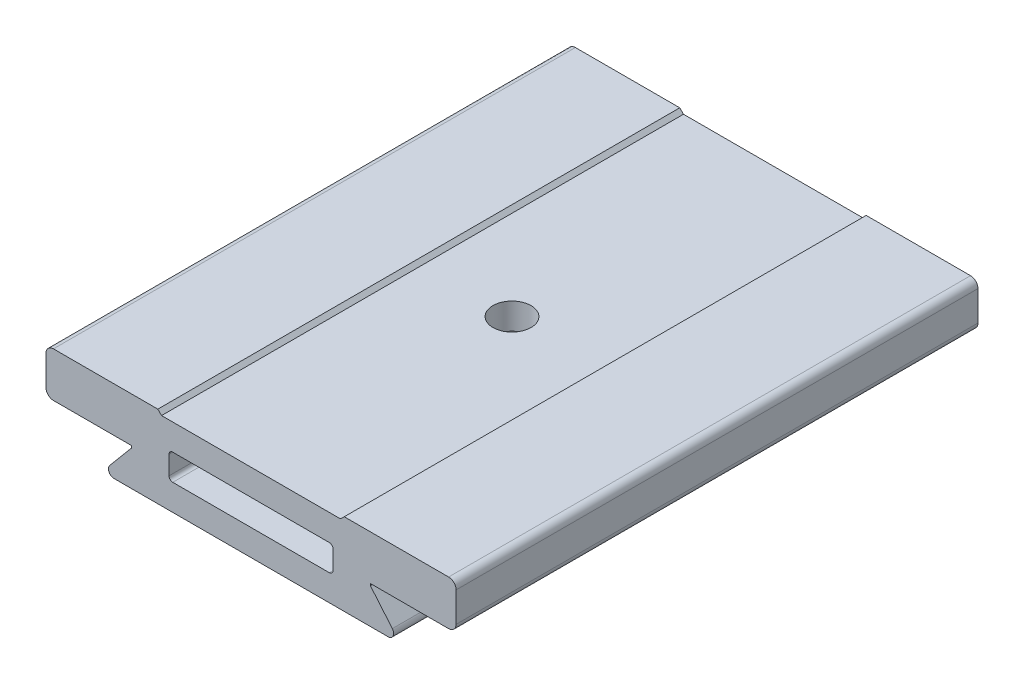
SolidWorks part; units mm, degrees
ref_plane "Front Plane" through (0, 0, 0) normal (0, 0, 1) x (1, 0, 0)
ref_plane "Top Plane" through (0, 0, 0) normal (0, 1, 0) x (1, 0, 0)
ref_plane "Right Plane" through (0, 0, 0) normal (1, 0, 0) x (0, 0, -1)
sketch "Sketch1" plane through (0, 0, 0) normal (0, 0, 1) x (1, 0, 0)
  line L1 (-27.5, 5.5) -> (27.5, 5.5)
  line L2 (-27.5, 5.5) -> (-27.5, -5.5)
  line L3 (-27.5, -5.5) -> (27.5, -5.5)
  line L4 (27.5, 5.5) -> (27.5, -5.5)
  line L5 (-27.5, 5.5) -> (27.5, -5.5) construction
  line L6 (-27.5, -5.5) -> (27.5, 5.5) construction
  point P0 (0, 0)
  dimension "D1" = 55
  dimension "D2" = 11
extrude "Boss-Extrude1" add sketch "Sketch1" along normal mid plane 70
sketch "Sketch2" plane through (0, 0, 35) normal (0, 0, 1) x (1, 0, 0)
  line L0 (-27.5, -0.5) -> (-16, -0.5)
  line L1 (-27.5, 5.5) -> (-27.5, -5.5) construction
  line L2 (-16, -0.5) -> (-16, -0.75)
  line L3 (-16, -0.75) -> (-18.9519, -4.2679)
  line L5 (-27.5, -5.5) -> (-18.3773, -5.5)
  line L6 (-27.5, -5.5) -> (-27.5, -0.5)
  line L7 (27.5, 5.5) -> (-27.5, 5.5) construction
  line L8 (-27.5, -5.5) -> (27.5, -5.5) construction
  arc A0 (-18.3773, -5.5) -> (-18.9519, -4.2679) centre (-18.3773, -4.75) cw
  dimension "D5" = 0.75
  dimension "D1" = 6
  dimension "D2" = 0.25
  dimension "D3" = 50
  dimension "D4" = 11.5
  dimension "D6" = 8.3727
extrude "Cut-Extrude1" cut sketch "Sketch2" against normal through all
mirror "Mirror1" about plane through (0, 0, 0) normal (1, 0, 0) of "Cut-Extrude1"
fillet "Fillet1" radius 1 4 edges at (27.5, 5.5, 0) (27.5, -0.5, 0) (-27.5, 5.5, 0) (-27.5, -0.5, 0)
sketch "Sketch3" plane through (0, 0, 35) normal (0, 0, 1) x (1, 0, 0)
  line L0 (0, 5.5) -> (0, -5.5) construction
  line L1 (26.5, 5.5) -> (-26.5, 5.5) construction
  line L2 (-18.3773, -5.5) -> (18.3773, -5.5) construction
  line L3 (-12.5, 5.5) -> (0, 5.5)
  line L4 (0, 5.5) -> (0, 5)
  line L5 (0, 5) -> (-12, 5)
  line L6 (-12, 5) -> (-12.5, 5.5)
  line L7 (-27.5, 4.5) -> (-27.5, 0.5) construction
  dimension "D1" = 15
  dimension "D2" = 135
  dimension "D3" = 0.5
extrude "Cut-Extrude2" cut sketch "Sketch3" against normal through all
mirror "Mirror2" about plane through (0, 0, 0) normal (1, 0, 0) of "Cut-Extrude2"
sketch "Sketch4" plane through (0, 0, 35) normal (0, 0, 1) x (1, 0, 0)
  line L0 (0, 5) -> (0, -5.5) construction
  line L1 (-12, 5) -> (12, 5) construction
  line L2 (-18.3773, -5.5) -> (18.3773, -5.5) construction
  line L4 (-11, 1.5) -> (11, 1.5)
  line L5 (-11, 1.5) -> (-11, -1.5)
  line L6 (-10.5, -2) -> (10.5, -2)
  line L7 (11, 1.5) -> (11, -1.5)
  line L8 (-11, 1.5) -> (11, -2) construction
  line L9 (-11, -2) -> (11, 1.5) construction
  arc A0 (10.5, -2) -> (11, -1.5) centre (10.5, -1.5) ccw
  arc A2 (-10.5, -2) -> (-11, -1.5) centre (-10.5, -1.5) cw
  point P6 (0, -0.25)
  dimension "D4" = 0.5
  dimension "D1" = 3.5
  dimension "D2" = 3.5
  dimension "D3" = 22
extrude "Cut-Extrude3" cut sketch "Sketch4" against normal through all
sketch "Sketch5" plane through (0, -5.5, 0) normal (0, -1, 0) x (1, 0, 0)
  line L1 (-8, 28.5) -> (8, 28.5)
  line L2 (-11, 25.5) -> (-11, -25.5)
  line L3 (-8, -28.5) -> (8, -28.5)
  line L4 (11, 25.5) -> (11, -25.5)
  line L5 (-11, 28.5) -> (11, -28.5) construction
  line L6 (-11, -28.5) -> (11, 28.5) construction
  arc A0 (-8, -28.5) -> (-11, -25.5) centre (-8, -25.5) cw
  arc A1 (8, -28.5) -> (11, -25.5) centre (8, -25.5) ccw
  arc A2 (11, 25.5) -> (8, 28.5) centre (8, 25.5) ccw
  arc A3 (-11, 25.5) -> (-8, 28.5) centre (-8, 25.5) cw
  point P0 (0, 0)
  dimension "D3" = 3
  dimension "D1" = 22
  dimension "D2" = 57
extrude "Cut-Extrude4" cut sketch "Sketch5" against normal up to surface (7 mm away) up to face at (0, 1.5, 0)
fillet "Fillet2" radius 0.5 2 edges at (11, 1.5, 0) (-11, 1.5, 0)
sketch "Sketch6" plane through (0, 1.5, 0) normal (0, -1, 0) x (1, 0, 0)
  circle A0 centre (0, 0) radius 2.5527
  dimension "D1" = 5.1054
extrude "Cut-Extrude5" cut sketch "Sketch6" against normal through all
cosmetic thread "Cosmetic Thread1" parameters "D2"=6.35
sketch "Sketch7" plane through (0, -5.5, 0) normal (0, -1, 0) x (1, 0, 0)
  circle A1 centre (-4.765, 43) radius 2.5 construction
  circle A2 centre (-4.765, 43) radius 12.5
  dimension "D3" = 5
  dimension "D4" = 25
  dimension "D1" = 43
  dimension "D2" = 4.765
extrude "Cut-Extrude6" [suppressed] cut sketch "Sketch7" against normal through all
sketch "Sketch8" plane through (0, 1.5, 0) normal (0, -1, 0) x (1, 0, 0)
  circle A0 centre (0, 0) radius 5.0419
  dimension "D1" = 10.0838
extrude "Cut-Extrude7" [suppressed] cut sketch "Sketch8" against normal through all
